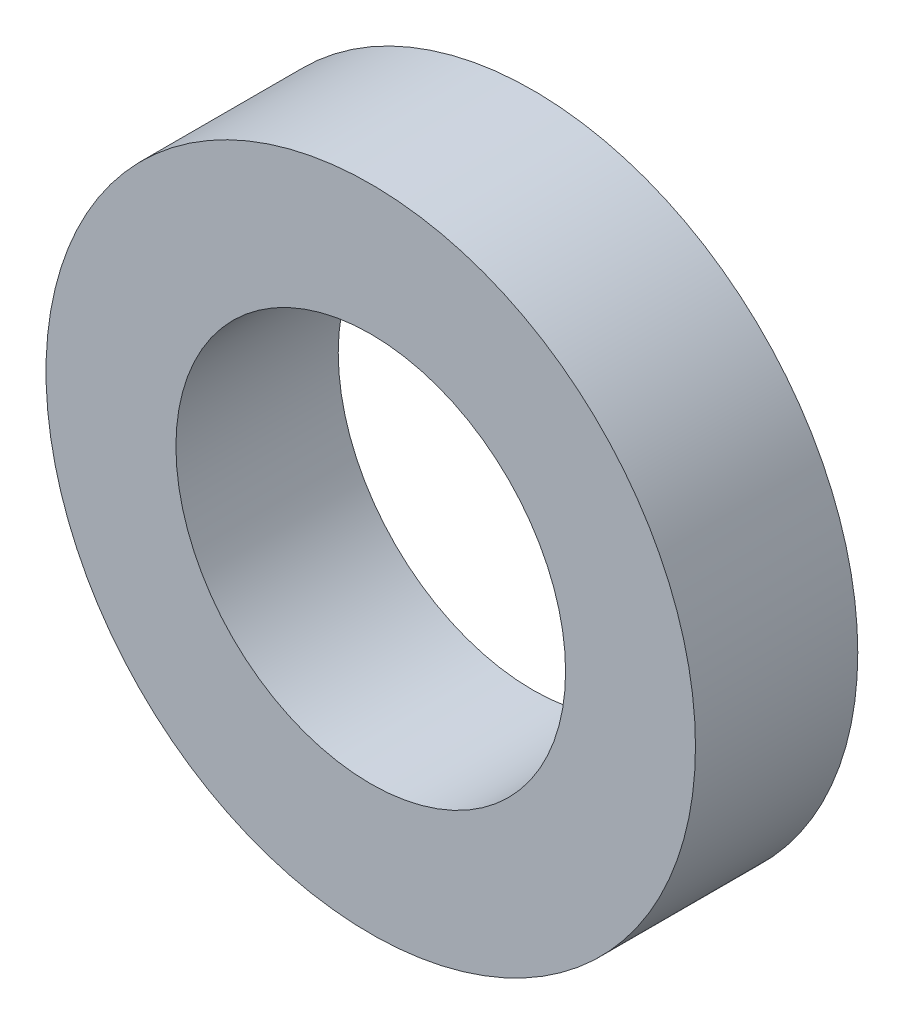
SolidWorks part; units mm, degrees
material "Cast Alloy Steel"
ref_plane "Front Plane" through (0, 0, 0) normal (0, 0, 1) x (1, 0, 0)
ref_plane "Top Plane" through (0, 0, 0) normal (0, 1, 0) x (1, 0, 0)
ref_plane "Right Plane" through (0, 0, 0) normal (1, 0, 0) x (0, 0, -1)
sketch "Sketch1" plane through (0, 0, 0) normal (0, 0, 1) x (1, 0, 0)
  circle A0 centre (0, 0) radius 7.9375
  circle A1 centre (0, 0) radius 4.7625
  dimension "D1" = 9.525
  dimension "D2" = 15.875
extrude "Boss-Extrude1" add sketch "Sketch1" along normal blind 3.9675
